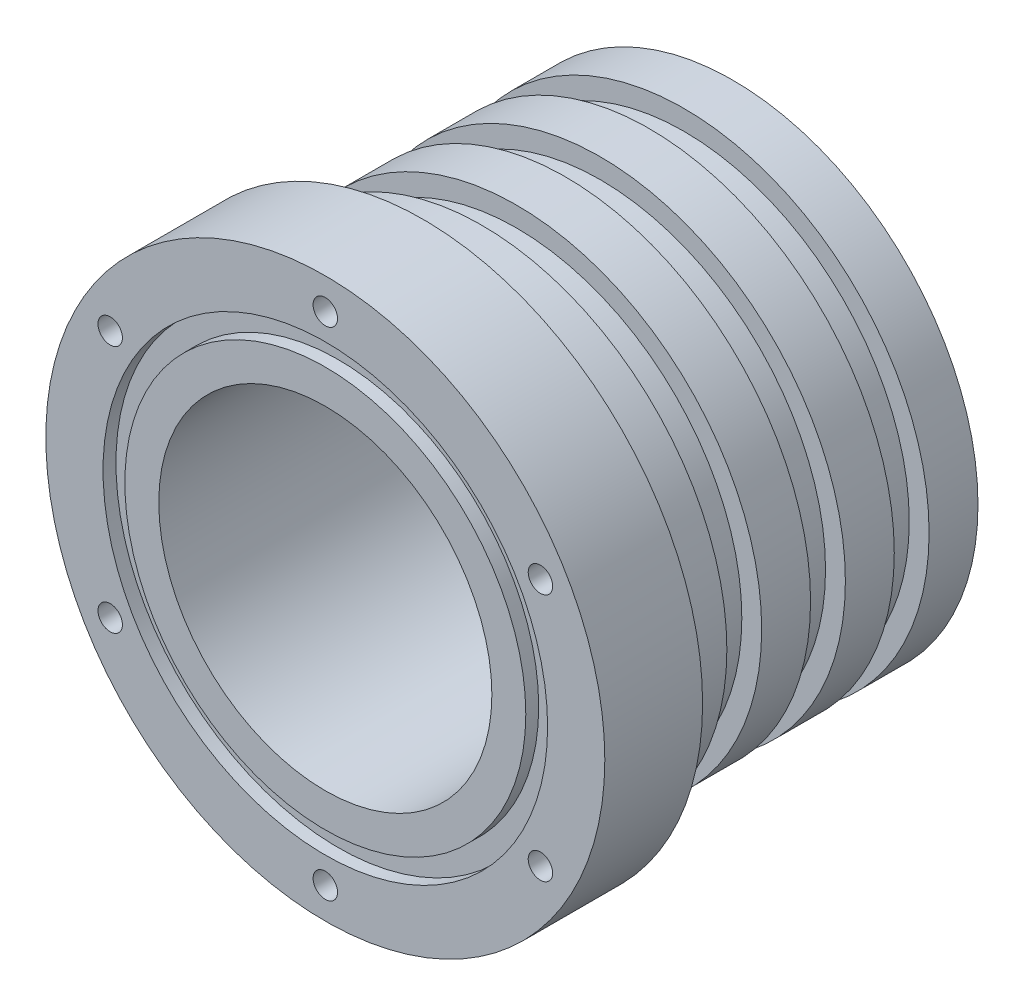
SolidWorks part; units mm, degrees
material "1060 Alloy"
ref_plane "Front Plane" through (0, 0, 0) normal (0, 0, 1) x (1, 0, 0)
ref_plane "Top Plane" through (0, 0, 0) normal (0, 1, 0) x (1, 0, 0)
ref_plane "Right Plane" through (0, 0, 0) normal (1, 0, 0) x (0, 0, -1)
sketch "Sketch1" plane through (0, 0, 0) normal (0, 1, 0) x (1, 0, 0)
  line L0 (-28.58, 0) -> (-28.58, 10)
  line L1 (-28.58, 10) -> (-25.06, 10)
  line L2 (-25.06, 10) -> (-25.06, 16)
  line L3 (-25.06, 16) -> (-23.03, 16)
  line L4 (-23.03, 16) -> (-23.03, 19.56)
  line L5 (-23.03, 19.56) -> (-25.06, 19.56)
  line L6 (-25.06, 19.56) -> (-25.06, 24.56)
  line L7 (-25.06, 24.56) -> (-23.03, 24.56)
  line L8 (-23.03, 24.56) -> (-23.03, 28.12)
  line L9 (-23.03, 28.12) -> (-25.06, 28.12)
  line L10 (-25.06, 28.12) -> (-25.06, 33.12)
  line L11 (-25.06, 33.12) -> (-23.03, 33.12)
  line L12 (-23.03, 33.12) -> (-23.03, 36.68)
  line L13 (-23.03, 36.68) -> (-25.06, 36.68)
  line L14 (-25.06, 36.68) -> (-25.06, 41.68)
  line L15 (-25.06, 41.68) -> (-17.03, 41.68)
  line L16 (-17.03, 41.68) -> (-17.03, 0)
  line L17 (-17.03, 0) -> (-28.58, 0)
  line L18 (0, 0) -> (0, 101.8418) construction
  dimension "D1" = 3.56
  dimension "D2" = 5
  dimension "D3" = 23.03
  dimension "D4" = 25.06
  dimension "D5" = 10
  dimension "D6" = 6
  dimension "D7" = 28.58
  dimension "D8" = 6
revolve "Revolve1" add sketch "Sketch1" angle 360 about L18
sketch "Sketch2" plane through (0, 0, 0) normal (0, 0, 1) x (1, 0, 0)
  circle A0 centre (0, 0) radius 25.4 construction
  point P3 (0, 25.4)
  point P7 (21.997, 12.7)
  point P8 (21.997, -12.7)
  point P9 (0, -25.4)
  point P10 (-21.997, -12.7)
  point P11 (-21.997, 12.7)
  point P16 (0, 0)
  dimension "D1" = 50.8
  dimension "D2" = 6
hole_wizard "M3x0.5 Tapped Hole1" positions "Sketch3" profile "Sketch4" tap size "M3x0.5" standard "ANSI Metric" end condition up to next
sketch "Sketch3" plane through (0, 0, 0) normal (0, 0, 1) x (1, 0, 0)
  point P0 (0, 25.4)
  point P3 (21.997, 12.7)
  point P6 (21.997, -12.7)
  point P9 (0, -25.4)
  point P12 (-21.997, -12.7)
  point P15 (-21.997, 12.7)
sketch "Sketch4" plane through (0, 25.4, 0) normal (1, 0, 0) x (0, -1, 0)
  line L0 (0, 0) -> (0, 10)
  line L1 (0, 10) -> (1.25, 10)
  line L2 (1.25, 10) -> (1.25, 0)
  line L5 (1.25, 0) -> (0, 0)
  line L11 (0, -6.35) -> (0, 107.95) construction
  dimension "Thru Tap Drill Dia." = 2.5
  dimension "Thru Tap Drill Depth" = 10
cosmetic thread "Hole Thread5" parameters "D2"=3
cosmetic thread "Hole Thread6" parameters "D2"=3
cosmetic thread "Hole Thread7" parameters "D2"=3
cosmetic thread "Hole Thread8" parameters "D2"=3
cosmetic thread "Hole Thread9" parameters "D2"=3
cosmetic thread "Hole Thread10" parameters "D2"=3
sketch "Sketch5" plane through (0, 0, 0) normal (0, 0, 1) x (1, 0, 0)
  circle A0 centre (0, 0) radius 22.73
  circle A1 centre (0, 0) radius 20.5
  dimension "D1" = 45.46
  dimension "D2" = 41
extrude "Cut-Extrude1" cut sketch "Sketch5" against normal blind 1.32
equation "\"D7@Sketch1\"=28.58"
